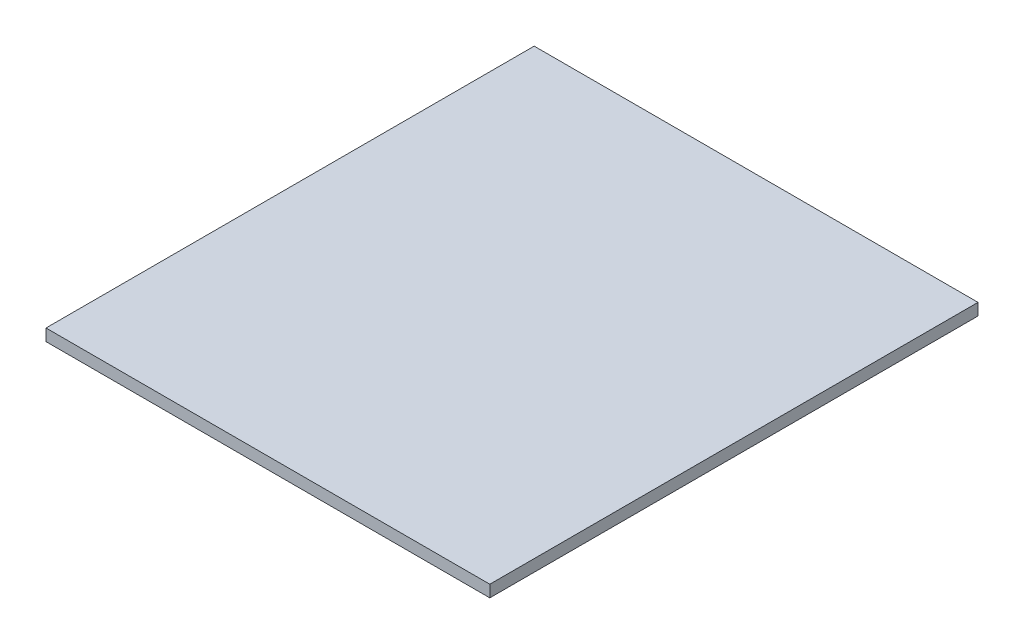
SolidWorks part; units mm, degrees
material "Cardboard"
ref_plane "Front Plane" through (0, 0, 0) normal (0, 0, 1) x (1, 0, 0)
ref_plane "Top Plane" through (0, 0, 0) normal (0, 1, 0) x (1, 0, 0)
ref_plane "Right Plane" through (0, 0, 0) normal (1, 0, 0) x (0, 0, -1)
sketch "Sketch1" plane through (0, 0, 0) normal (0, 1, 0) x (1, 0, 0)
  line L1 (0, 0) -> (150, 0)
  line L2 (0, 0) -> (0, 165)
  line L3 (0, 165) -> (150, 165)
  line L4 (150, 0) -> (150, 165)
  dimension "D1" = 165
  dimension "D2" = 150
extrude "Boss-Extrude1" add sketch "Sketch1" along normal blind 4
